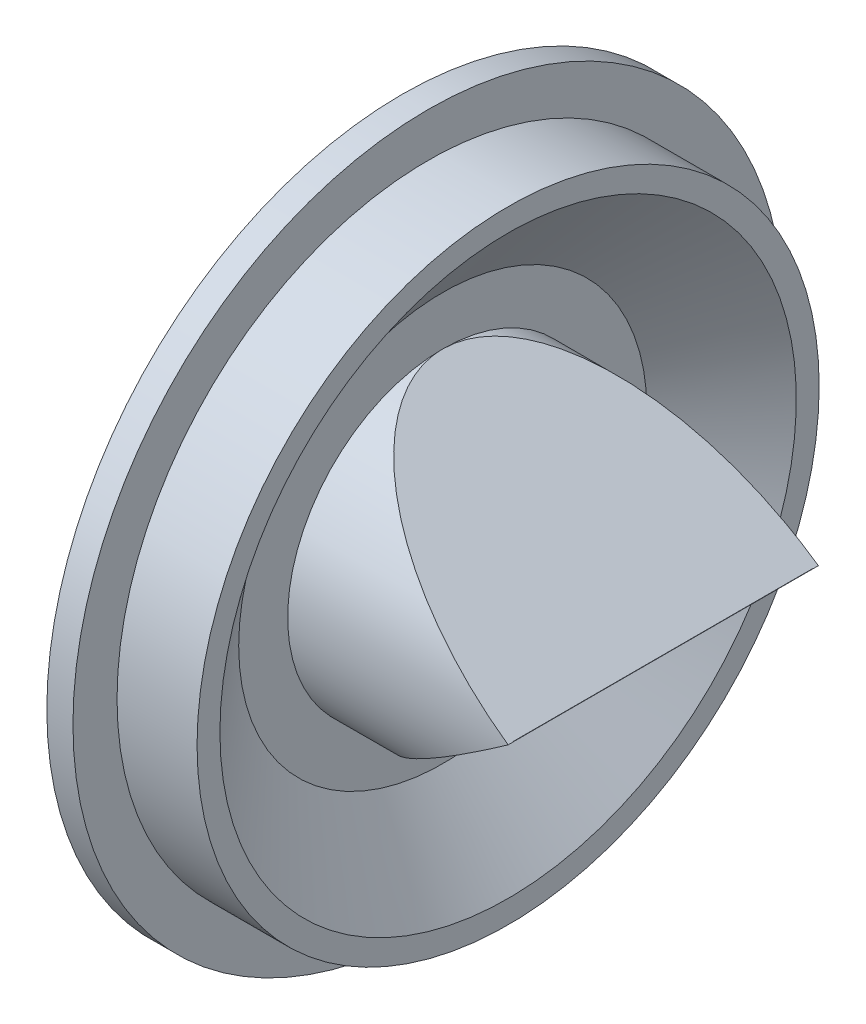
SolidWorks part; units mm, degrees
ref_plane "Front" through (0, 0, 0) normal (0, 0, 1) x (1, 0, 0)
ref_plane "Top" through (0, 0, 0) normal (0, 1, 0) x (1, 0, 0)
ref_plane "Right" through (0, 0, 0) normal (1, 0, 0) x (0, 0, -1)
sketch "Sketch3" plane through (0, 0, 0) normal (-1, 0, 0) x (0, 0, 1)
  circle A0 centre (0, 0) radius 9.5
extrude "Boss-Extrude1" add sketch "Sketch3" against normal blind 16
sketch "Sketch4" plane through (0, 0, 0) normal (0, 0, 1) x (1, 0, 0)
  line L0 (0, 0) -> (24.256, 0) construction
  line L2 (16, -9.5) -> (16, 9.5) construction
  line L7 (2.5, 9.5) -> (18.0589, 17.2679)
  line L8 (2.5, 9.5) -> (16, 0)
  line L11 (2.5, -9.5) -> (16, 0)
  line L12 (2.5, -9.5) -> (18.0589, -17.2679)
  line L13 (18.0589, -17.2679) -> (18.0589, 17.2679)
  point P11 (18.0589, 0)
extrude "Cut-Extrude1" cut sketch "Sketch4" against normal through all both and the other way through all
shell "Shell7" thickness 0.3
sketch "Sketch1" plane through (0, 0, 0) normal (0, 0, 1) x (1, 0, 0)
  line L0 (0, 18.75) -> (0, 21.75)
  line L1 (0, 21.75) -> (1.6, 21.75)
  line L2 (1.6, 21.75) -> (1.6, 19.05)
  line L3 (1.6, 19.05) -> (6.5, 19.05)
  line L4 (6.5, 19.05) -> (6.5, 17.65)
  line L5 (0, 18.75) -> (6.2, 18.75)
  line L6 (0, 0) -> (26.4761, 0) construction
  line L7 (6.5, 17.65) -> (2.5, 12.5)
  line L8 (2.5, 12.5) -> (2.5, 9.5)
  line L9 (6.2, 18.75) -> (6.2, 17.7528)
  line L10 (6.2, 17.7528) -> (2.2, 12.6028)
  line L11 (6.2, 19.05) -> (6.2, 17.7528) construction
  line L12 (2.2, 12.6028) -> (2.2, 9.5)
  line L13 (6.2, 17.7528) -> (2.2631, 12.684) construction
  line L14 (2.2, 12.5) -> (2.2, 9.5) construction
  line L15 (2.2, 9.5) -> (2.5, 9.5)
  dimension "D1" = 37.5
  dimension "D2" = 43.5
  dimension "D3" = 1.6
  dimension "D4" = 0.3
  dimension "D6" = 0.3
  dimension "D7" = 6.5
  dimension "D8" = 4
  dimension "D9" = 25
  dimension "D10" = 19
  dimension "D11" = 0.3
revolve "Revolve1" add sketch "Sketch1" angle 360 about L6
sketch "Sketch8" plane through (2.2, 0, 0) normal (-1, 0, 0) x (0, 0, 1)
  circle A0 centre (0, 0) radius 10.7058
extrude "Cut-Extrude5" cut sketch "Sketch8" along normal blind 10
sketch "Sketch9" plane through (2.2, 0, 0) normal (-1, 0, 0) x (0, 0, 1)
  line L2 (-9.2, -0.01) -> (9.2, -0.01)
  line L3 (-9.2, -0.01) -> (9.2, -0.01)
  line L5 (-9.2, 0.01) -> (9.2, 0.01)
  line L6 (-9.2, 0.01) -> (9.2, 0.01)
  arc A0 (-9.2, 0.01) -> (-9.2, -0.01) centre (0, 0) ccw
  arc A1 (9.2, -0.01) -> (9.2, 0.01) centre (0, 0) ccw
  dimension "D1" = 0.01
  dimension "D2" = 0.01
extrude "Cut-Extrude6" cut sketch "Sketch9" against normal blind 30
